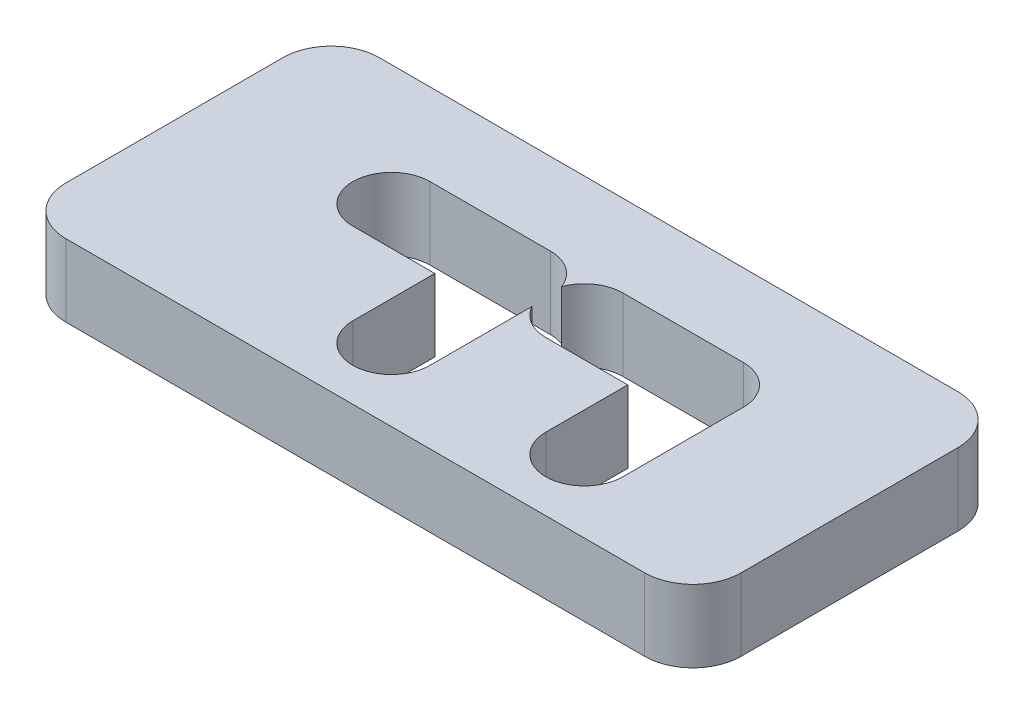
SolidWorks part; units mm, degrees
material "Beech"
ref_plane "Front Plane" through (0, 0, 0) normal (0, 0, 1) x (1, 0, 0)
ref_plane "Top Plane" through (0, 0, 0) normal (0, 1, 0) x (1, 0, 0)
ref_plane "Right Plane" through (0, 0, 0) normal (1, 0, 0) x (0, 0, -1)
sketch "Sketch1" plane through (0, 0, 0) normal (0, 1, 0) x (1, 0, 0)
  line L0 (6.5, 15) -> (6.5, 10) construction
  line L1 (-14, -15) -> (14, -15)
  line L2 (-14, -15) -> (-14, 15)
  line L3 (-14, 15) -> (14, 15)
  line L4 (14, -15) -> (14, 15)
  line L5 (-14, -15) -> (14, 15) construction
  line L6 (-14, 15) -> (14, -15) construction
  line L7 (6.5, 10) -> (-1.5, 10) construction
  line L8 (6.5, 10) -> (2.4061, 5.6137) construction
  line L9 (7.6697, 8.9083) -> (3.5758, 4.522) construction
  line L10 (5.3303, 11.0917) -> (1.2364, 6.7054) construction
  line L11 (-1.5, 10) -> (-5.5939, 5.6137) construction
  line L12 (-0.3303, 8.9083) -> (-4.4242, 4.522) construction
  line L13 (-2.6697, 11.0917) -> (-6.7636, 6.7054) construction
  line L14 (-1.5, 10) -> (-1.5, 5) construction
  line L15 (0.1, 10) -> (0.1, 5)
  line L16 (-3.1, 10) -> (-3.1, 5)
  line L17 (6.5, 10) -> (6.5, 5) construction
  line L18 (8.1, 10) -> (8.1, 5)
  line L19 (4.9, 10) -> (4.9, 5)
  line L20 (6.5, 10) -> (1.5, 10) construction
  line L21 (6.5, 8.4) -> (1.5, 8.4)
  line L22 (6.5, 11.6) -> (1.5, 11.6)
  line L23 (-1.5, 10) -> (-6.5, 10) construction
  line L24 (-1.5, 8.4) -> (-6.5, 8.4)
  line L25 (-1.5, 11.6) -> (-6.5, 11.6)
  line L26 (6.5, 10) -> (14, 10) construction
  line L27 (-6.5, 10) -> (-14, 10) construction
  circle A0 centre (6.5, 10) radius 1.6 construction
  circle A1 centre (-1.5, 10) radius 1.6 construction
  arc A2 (7.6697, 8.9083) -> (5.3303, 11.0917) centre (6.5, 10) ccw construction
  arc A3 (1.2364, 6.7054) -> (3.5758, 4.522) centre (2.4061, 5.6137) ccw construction
  arc A4 (-0.3303, 8.9083) -> (-2.6697, 11.0917) centre (-1.5, 10) ccw construction
  arc A5 (-6.7636, 6.7054) -> (-4.4242, 4.522) centre (-5.5939, 5.6137) ccw construction
  arc A6 (0.1, 10) -> (-3.1, 10) centre (-1.5, 10) ccw
  arc A7 (-3.1, 5) -> (0.1, 5) centre (-1.5, 5) ccw
  arc A8 (8.1, 10) -> (4.9, 10) centre (6.5, 10) ccw
  arc A9 (4.9, 5) -> (8.1, 5) centre (6.5, 5) ccw
  arc A10 (6.5, 8.4) -> (6.5, 11.6) centre (6.5, 10) ccw
  arc A11 (1.5, 11.6) -> (1.5, 8.4) centre (1.5, 10) ccw
  arc A12 (-1.5, 8.4) -> (-1.5, 11.6) centre (-1.5, 10) ccw
  arc A13 (-6.5, 11.6) -> (-6.5, 8.4) centre (-6.5, 10) ccw
  point P0 (0, 0)
  point P11 (4.453, 7.8068)
  point P17 (-3.547, 7.8068)
  point P25 (-1.5, 7.5)
  point P30 (6.5, 7.5)
  point P39 (4, 10)
  point P44 (-4, 10)
  dimension "D5" = 3.2
  dimension "D6" = 6
  dimension "D8" = 8
  dimension "D10" = 5
  dimension "D1" = 28
  dimension "D2" = 30
  dimension "D3" = 5
  dimension "D7" = 6
  dimension "D9" = 5
  dimension "D11" = 5
extrude "Boss-Extrude1" add sketch "Sketch1" along normal blind 3 contours L1 L4 L3 L2 A13 L25 A6 A11 L22 A2 L18 A9 L19 L9 A3 L10 L21 L15 A7 L16 L12 A5 L13 L24
sketch "Sketch2" plane through (0, 3, 0) normal (0, 1, 0) x (1, 0, 0)
  line L0 (-5.25, -15) -> (-5.25, -10) construction
  line L1 (-14, -15) -> (14, -15) construction
  line L2 (0, -15) -> (0, 0) construction
  line L3 (14, 0) -> (8.5, -15)
  line L4 (14, -15) -> (14, 15) construction
  line L5 (8.5, -15) -> (14, -15)
  line L6 (14, -15) -> (14, 0)
  line L7 (-8.5, -15) -> (-14, -15)
  line L8 (-14, -15) -> (-14, 0)
  line L9 (-14, 0) -> (-8.5, -15)
  circle A0 centre (-5.25, -10) radius 1.6
  circle A1 centre (5.25, -10) radius 1.6
  point P4 (0, -15)
  dimension "D3" = 3.2
  dimension "D1" = 5.25
  dimension "D2" = 5
  dimension "D4" = 5.5
extrude "Cut-Extrude1" cut sketch "Sketch2" against normal through all
sketch "Sketch3" plane through (0, 3, 0) normal (0, 1, 0) x (1, 0, 0)
  line L0 (-14, 0) -> (-14, 15) construction
  line L1 (-14, 2) -> (14, 2)
  line L2 (-14, 2) -> (-14, -15)
  line L3 (-14, -15) -> (14, -15)
  line L4 (14, 2) -> (14, -15)
  line L5 (-14, 15) -> (14, 15) construction
  line L6 (14, 0) -> (14, 15) construction
  line L7 (-8.5, -15) -> (8.5, -15) construction
  dimension "D1" = 13
extrude "Cut-Extrude2" cut sketch "Sketch3" against normal through all
fillet "Fillet1" radius 2 4 edges at (-14, 1.5, -2) (14, 1.5, -2) (14, 1.5, -15) (-14, 1.5, -15)
